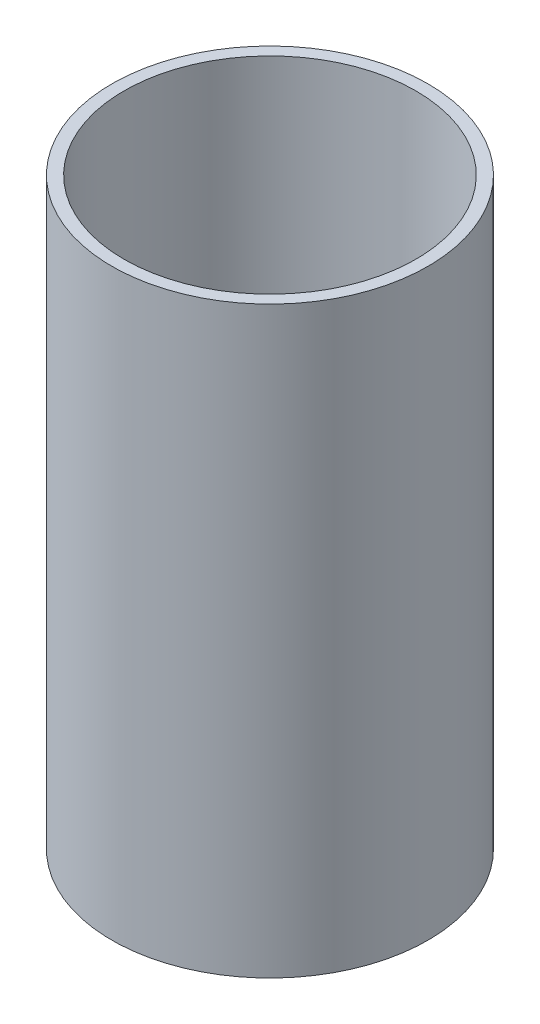
SolidWorks part; units mm, degrees
ref_plane "Front Plane" through (0, 0, 0) normal (0, 0, 1) x (1, 0, 0)
ref_plane "Top Plane" through (0, 0, 0) normal (0, 1, 0) x (1, 0, 0)
ref_plane "Right Plane" through (0, 0, 0) normal (1, 0, 0) x (0, 0, -1)
sketch "Sketch1" plane through (0, 0, 0) normal (0, 0, 1) x (1, 0, 0)
  line L0 (-38.1, 0) -> (-38.1, 152.4)
  line L1 (-38.1, 152.4) -> (-41.275, 152.4)
  line L2 (-41.275, 152.4) -> (-41.275, 0)
  line L3 (-41.275, 0) -> (-38.1, 0)
  line L4 (0, 0) -> (0, 74.5902) construction
  dimension "D1" = 38.1
  dimension "D2" = 41.275
  dimension "D3" = 152.4
revolve "Revolve1" add sketch "Sketch1" angle 360 about L4
